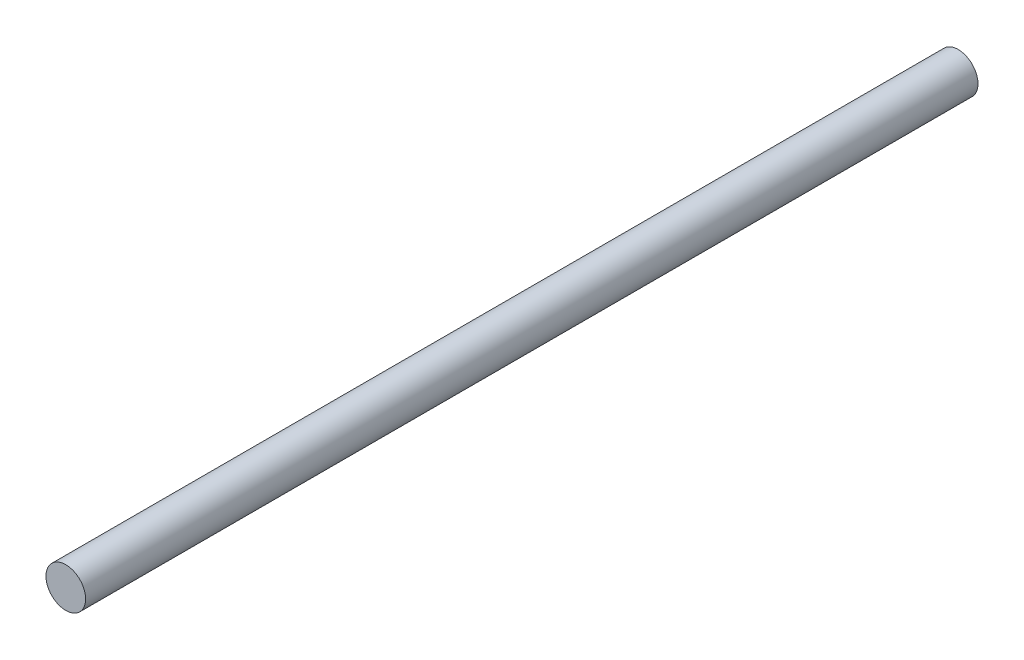
SolidWorks part; units mm, degrees
ref_plane "Front Plane" through (0, 0, 0) normal (0, 0, 1) x (1, 0, 0)
ref_plane "Top Plane" through (0, 0, 0) normal (0, 1, 0) x (1, 0, 0)
ref_plane "Right Plane" through (0, 0, 0) normal (1, 0, 0) x (0, 0, -1)
sketch "Sketch2" plane through (0, 0, 0) normal (0, 0, 1) x (1, 0, 0)
  circle A0 centre (0, 0) radius 4
extrude "Boss-Extrude1" add sketch "Sketch2" along normal blind 180
